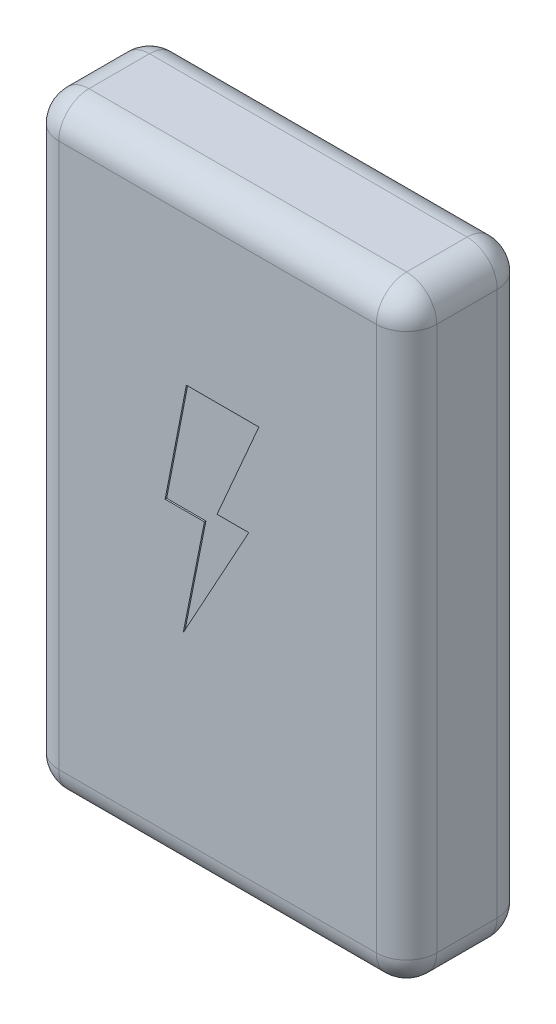
SolidWorks part; units mm, degrees
ref_plane "Front" through (0, 0, 0) normal (0, 0, 1) x (1, 0, 0)
ref_plane "Top" through (0, 0, 0) normal (0, 1, 0) x (1, 0, 0)
ref_plane "Right" through (0, 0, 0) normal (1, 0, 0) x (0, 0, -1)
sketch "Sketch1" plane through (0, 0, 0) normal (0, 0, 1) x (1, 0, 0)
  line L1 (-12.5, -20) -> (12.5, -20)
  line L2 (-12.5, -20) -> (-12.5, 20)
  line L3 (-12.5, 20) -> (12.5, 20)
  line L4 (12.5, -20) -> (12.5, 20)
  line L5 (-12.5, -20) -> (12.5, 20) construction
  line L6 (-12.5, 20) -> (12.5, -20) construction
  point P0 (0, 0)
  dimension "D1" = 25
  dimension "D2" = 40
extrude "Boss-Extrude1" add sketch "Sketch1" along normal blind 8
fillet "Fillet1" radius 2 12 edges at (0, 20, 0) (-12.5, 0, 0) (0, -20, 0) (12.5, 0, 0) (0, -20, 8) (-12.5, 0, 8) (0, 20, 8) (12.5, 0, 8) (-12.5, -20, 4) (12.5, -20, 4) (12.5, 20, 4) (-12.5, 20, 4)
sketch "Sketch2" plane through (0, 0, 8) normal (0, 0, 1) x (1, 0, 0)
  line L0 (-2.061, 8.2374) -> (2.7366, 8.2374)
  line L1 (2.7366, 8.2374) -> (-0.0318, 1.8542)
  line L2 (-0.0318, 1.8542) -> (2.0682, 1.8542)
  line L3 (2.0682, 1.8542) -> (-2.2684, -6.0397)
  line L4 (-2.2684, -6.0397) -> (-0.8676, 1.0031)
  line L5 (-0.8676, 1.0031) -> (-3.4643, 1.0031)
  line L6 (-3.4643, 1.0031) -> (-2.061, 8.2374)
  point P6 (1.6224, 7.5687)
  point P8 (2.7366, 8.2374)
  point P9 (-3.4643, 1.0031)
extrude "Cut-Extrude1" cut sketch "Sketch2" against normal blind 0.1
